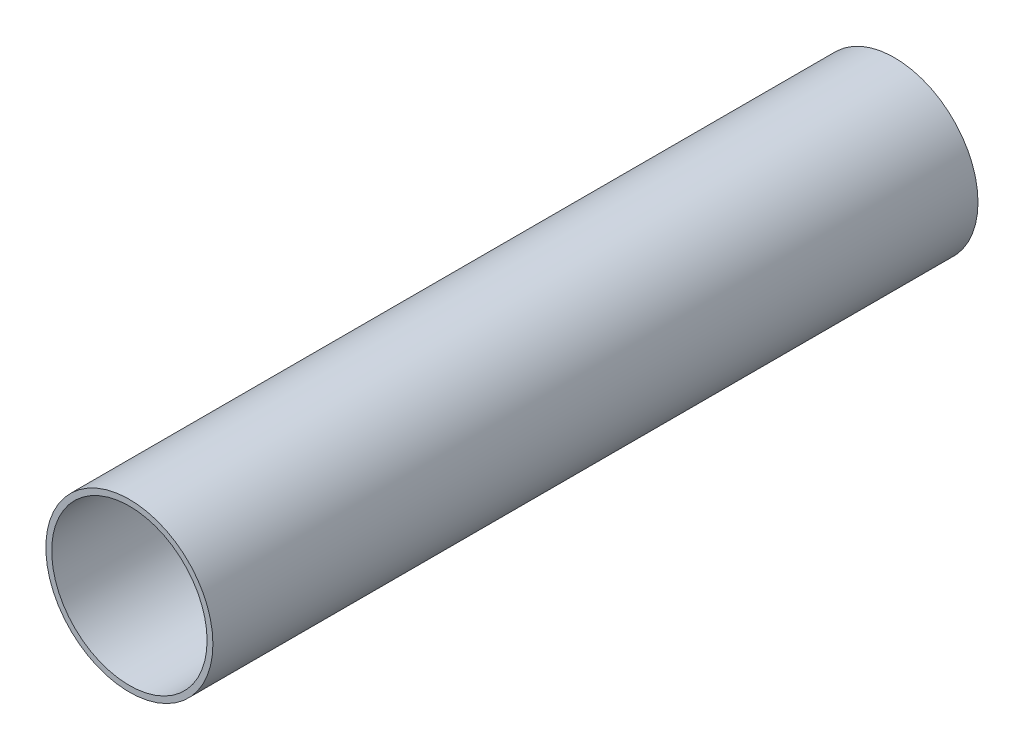
SolidWorks part; units mm, degrees
ref_plane "Front Plane" through (0, 0, 0) normal (0, 0, 1) x (1, 0, 0)
ref_plane "Top Plane" through (0, 0, 0) normal (0, 1, 0) x (1, 0, 0)
ref_plane "Right Plane" through (0, 0, 0) normal (1, 0, 0) x (0, 0, -1)
sketch "Sketch1" plane through (0, 0, 0) normal (0, 0, 1) x (1, 0, 0)
  circle A0 centre (0, 0) radius 20.6375
  circle A1 centre (0, 0) radius 22.1869
extrude "Boss-Extrude1" add sketch "Sketch1" along normal blind 203.2
